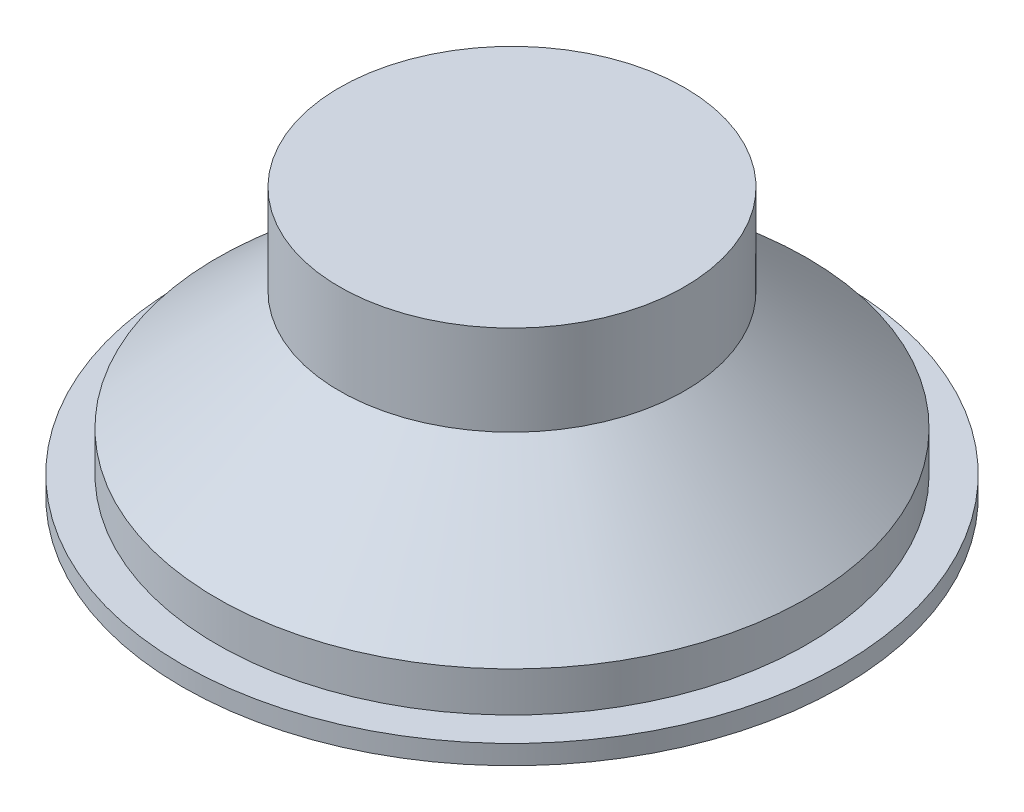
SolidWorks part; units mm, degrees
ref_plane "Спереди" through (0, 0, 0) normal (0, 0, 1) x (1, 0, 0)
ref_plane "Сверху" through (0, 0, 0) normal (0, 1, 0) x (1, 0, 0)
ref_plane "Справа" through (0, 0, 0) normal (1, 0, 0) x (0, 0, -1)
sketch "Эскиз1" plane through (0, 0, 0) normal (1, 0, 0) x (0, 0, -1)
  line L0 (-107.5, 0) -> (-128, 0)
  line L1 (-128, 0) -> (-128, 7.5)
  line L2 (-128, 7.5) -> (-114.5, 7.5)
  line L3 (-114.5, 7.5) -> (-114.5, 23)
  line L4 (-62, 69) -> (-67, 69)
  line L5 (-67, 69) -> (-67, 104)
  line L6 (-67, 104) -> (0, 104)
  line L7 (0, 0) -> (0, 104) construction
  line L8 (-107.5, 0) -> (-30, 50)
  line L9 (-30, 50) -> (0, 50)
  line L10 (-114.5, 23) -> (-62, 69)
  line L11 (0, 0) -> (-107.5, 0) construction
  line L12 (0, 104) -> (0, 50)
  line L13 (0, 50) -> (0, 104)
  dimension "D1" = 256
  dimension "D2" = 229
  dimension "D3" = 215
  dimension "D4" = 50
  dimension "D5" = 60
  dimension "D6" = 7.5
  dimension "D7" = 23
  dimension "D8" = 134
  dimension "D9" = 104
  dimension "D10" = 35
  dimension "D11" = 5
revolve "Повернуть1" add sketch "Эскиз1" angle 360 about L7
